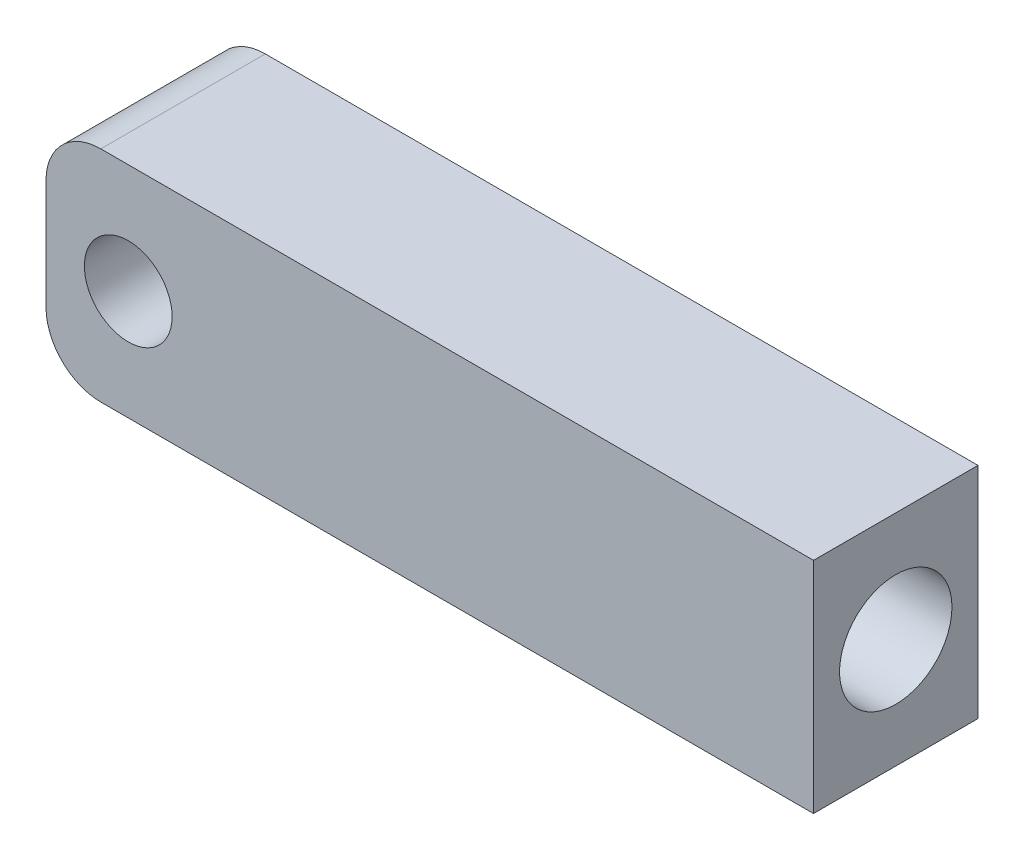
SolidWorks part; units mm, degrees
ref_plane "前视基准面" through (0, 0, 0) normal (0, 0, 1) x (1, 0, 0)
ref_plane "上视基准面" through (0, 0, 0) normal (0, 1, 0) x (1, 0, 0)
ref_plane "右视基准面" through (0, 0, 0) normal (1, 0, 0) x (0, 0, -1)
sketch "草图2" plane through (0, 0, 0) normal (0, 0, 1) x (1, 0, 0)
  line L0 (0, 2) -> (0, 6)
  line L1 (2, 8) -> (28, 8)
  line L2 (28, 8) -> (28, 0)
  line L3 (28, 0) -> (2, 0)
  arc A0 (0, 2) -> (2, 0) centre (2, 2) ccw
  arc A1 (0, 6) -> (2, 8) centre (2, 6) cw
  circle A2 centre (3, 4) radius 1.6
  point P7 (0, 0)
  dimension "D1" = 2
extrude "凸台-拉伸1" add sketch "草图2" along normal blind 6
sketch "草图3" plane through (28, 0, 0) normal (1, 0, 0) x (0, 0, -1)
  circle A0 centre (-3, 4) radius 2.05
extrude "切除-拉伸1" cut sketch "草图3" against normal blind 20
